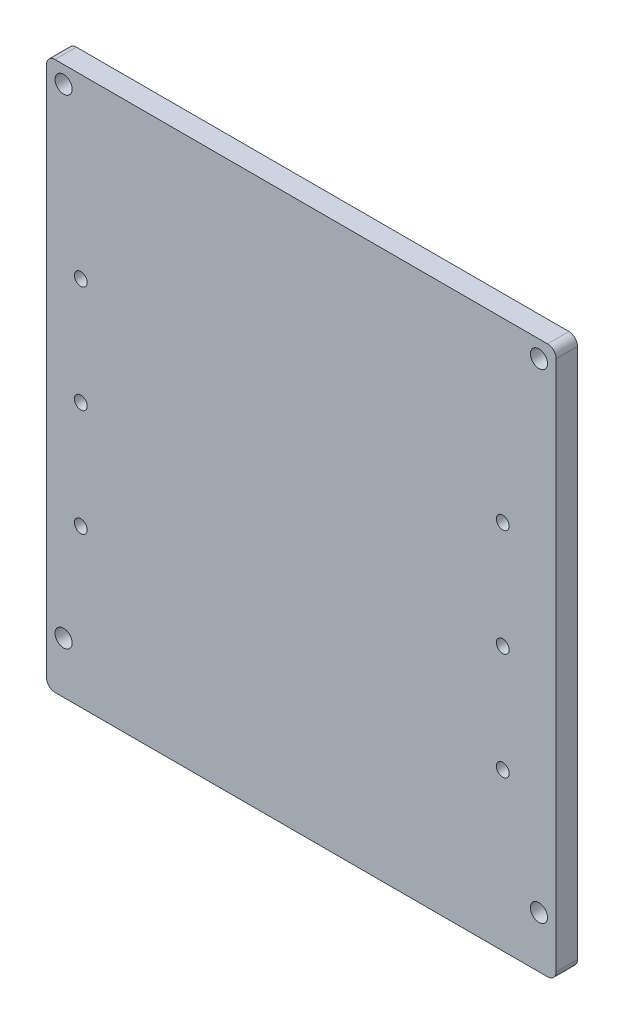
SolidWorks part; units mm, degrees
ref_plane "前视基准面" through (0, 0, 0) normal (0, 0, 1) x (1, 0, 0)
ref_plane "上视基准面" through (0, 0, 0) normal (0, 1, 0) x (1, 0, 0)
ref_plane "右视基准面" through (0, 0, 0) normal (1, 0, 0) x (0, 0, -1)
other "Configuration Table"
sketch "草图1" plane through (0, 0, 0) normal (0, 0, 1) x (1, 0, 0)
  line L8 (62.7093, -58.3451) -> (62.7093, 57.6549)
  line L13 (60.7093, 59.6549) -> (-54.2907, 59.6549)
  line L14 (-56.2907, 57.6549) -> (-56.2907, -58.3451)
  line L15 (-54.2907, -60.3451) -> (60.7093, -60.3451)
  arc A12 (62.7093, 57.6549) -> (60.7093, 59.6549) centre (60.7093, 57.6549) ccw
  arc A13 (-54.2907, 59.6549) -> (-56.2907, 57.6549) centre (-54.2907, 57.6549) ccw
  arc A14 (-56.2907, -58.3451) -> (-54.2907, -60.3451) centre (-54.2907, -58.3451) ccw
  arc A15 (60.7093, -60.3451) -> (62.7093, -58.3451) centre (60.7093, -58.3451) ccw
  circle A16 centre (-52.2907, -56.3451) radius 2
  circle A17 centre (58.7093, -56.3451) radius 2
  circle A18 centre (58.7093, 55.6549) radius 2
  circle A19 centre (-52.2907, 55.6549) radius 2
  point P0 (0, 0)
extrude "凸台-拉伸1" add sketch "草图1" along normal blind 5
sketch "草图5" plane through (0, 0, 3) normal (0, 0, 1) x (1, 0, 0)
  line L36 (-56.2756, 57.6214) -> (-56.2756, -74.02) construction
  line L37 (56.3281, 59.5462) -> (-54.3508, 59.5462) construction
  line L38 (-56.4727, -58.129) -> (58.5273, -58.129) construction
  line L44 (-56.2756, 24.5462) -> (58.253, 24.5462) construction
  line L45 (-56.2756, 57.6214) -> (-56.2756, -74.02) construction
  line L46 (58.253, -74.02) -> (58.253, 57.6214) construction
  line L49 (-31.2756, 59.5462) -> (-31.2756, -58.129) construction
  line L50 (38.253, 59.5462) -> (38.253, -58.129) construction
  line L51 (33.2648, -15.6264) -> (33.2648, 0.4736)
  line L52 (17.1648, -15.6264) -> (33.2648, -15.6264)
  line L53 (17.1648, 0.4736) -> (17.1648, -15.6264)
  line L54 (33.2648, 0.4736) -> (17.1648, 0.4736)
  line L55 (33.2648, 6.3736) -> (33.2648, 22.4736)
  line L56 (17.1648, 6.3736) -> (33.2648, 6.3736)
  line L57 (17.1648, 22.4736) -> (17.1648, 6.3736)
  line L58 (33.2648, 22.4736) -> (17.1648, 22.4736)
  line L59 (11.2648, -15.6264) -> (11.2648, 0.4736)
  line L60 (-4.8352, -15.6264) -> (11.2648, -15.6264)
  line L61 (-4.8352, 0.4736) -> (-4.8352, -15.6264)
  line L62 (11.2648, 0.4736) -> (-4.8352, 0.4736)
  line L63 (-10.7352, 6.3736) -> (-10.7352, 22.4736)
  line L64 (-26.8352, 6.3736) -> (-10.7352, 6.3736)
  line L65 (-26.8352, 22.4736) -> (-26.8352, 6.3736)
  line L66 (-10.7352, 22.4736) -> (-26.8352, 22.4736)
  line L67 (-10.7352, -15.6264) -> (-10.7352, 0.4736)
  line L68 (-26.8352, -15.6264) -> (-10.7352, -15.6264)
  line L69 (-26.8352, 0.4736) -> (-26.8352, -15.6264)
  line L70 (-10.7352, 0.4736) -> (-26.8352, 0.4736)
  line L71 (-10.7352, -37.6264) -> (-10.7352, -21.5264)
  line L72 (-26.8352, -37.6264) -> (-10.7352, -37.6264)
  line L73 (-26.8352, -21.5264) -> (-26.8352, -37.6264)
  line L74 (-10.7352, -21.5264) -> (-26.8352, -21.5264)
  line L75 (11.2648, 6.3736) -> (11.2648, 22.4736)
  line L76 (-4.8352, 6.3736) -> (11.2648, 6.3736)
  line L77 (-4.8352, 22.4736) -> (-4.8352, 6.3736)
  line L78 (11.2648, 22.4736) -> (-4.8352, 22.4736)
  line L79 (11.2648, -37.6264) -> (11.2648, -21.5264)
  line L80 (-4.8352, -37.6264) -> (11.2648, -37.6264)
  line L81 (-4.8352, -21.5264) -> (-4.8352, -37.6264)
  line L82 (11.2648, -21.5264) -> (-4.8352, -21.5264)
  line L83 (33.2648, -37.6264) -> (33.2648, -21.5264)
  line L84 (17.1648, -37.6264) -> (33.2648, -37.6264)
  line L85 (17.1648, -21.5264) -> (17.1648, -37.6264)
  line L86 (33.2648, -21.5264) -> (17.1648, -21.5264)
  line L87 (-56.2756, -40.0764) -> (58.253, -40.0764) construction
  line L88 (33.2648, -58.6264) -> (17.1648, -58.6264)
  line L89 (17.1648, -58.6264) -> (17.1648, -42.5264)
  line L90 (17.1648, -42.5264) -> (33.2648, -42.5264)
  line L91 (33.2648, -42.5264) -> (33.2648, -58.6264)
  line L92 (11.2648, -58.6264) -> (-4.8352, -58.6264)
  line L93 (-4.8352, -58.6264) -> (-4.8352, -42.5264)
  line L94 (-4.8352, -42.5264) -> (11.2648, -42.5264)
  line L95 (11.2648, -42.5264) -> (11.2648, -58.6264)
  line L96 (-10.7352, -58.6264) -> (-26.8352, -58.6264)
  line L97 (-26.8352, -58.6264) -> (-26.8352, -42.5264)
  line L98 (-26.8352, -42.5264) -> (-10.7352, -42.5264)
  line L99 (-10.7352, -42.5264) -> (-10.7352, -58.6264)
  line L100 (58.253, -74.02) -> (58.253, 57.6214) construction
  circle A0 centre (-48.2756, 18.3019) radius 1.5
  circle A1 centre (50.253, 18.3019) radius 1.5
  circle A2 centre (-48.2756, -6.6981) radius 1.5
  circle A3 centre (50.253, -6.6981) radius 1.5
  circle A4 centre (-48.2756, -31.6981) radius 1.5
  circle A5 centre (50.253, -31.6981) radius 1.5
  dimension "D5" = 25
  dimension "D14" = 3
  dimension "D15" = 3
  dimension "D16" = 3
  dimension "D17" = 3
  dimension "D18" = 3
  dimension "D19" = 3
  dimension "D1" = 35
  dimension "D2" = 25
  dimension "D3" = 20
  dimension "D4" = 2.45
  dimension "D6" = 25
  dimension "D7" = 25
  dimension "D8" = 25
  dimension "D9" = 8
  dimension "D10" = 8
  dimension "D11" = 8
  dimension "D12" = 8
  dimension "D13" = 101.6508
extrude "切除-拉伸1" cut sketch "草图5" against normal through all
sketch "草图8" plane through (0, 0, 5) normal (0, 0, 1) x (1, 0, 0)
  line L0 (-26.8352, -42.5264) -> (-26.8352, -58.6264) construction
  line L1 (-56.2907, -58.3451) -> (-26.8352, -58.3451)
  line L2 (-56.2907, -58.3451) -> (-56.2907, -68.3451)
  line L3 (-56.2907, -68.3451) -> (-26.8352, -68.3451)
  line L4 (-26.8352, -58.3451) -> (-26.8352, -60.3451)
  line L5 (-54.2907, -60.3451) -> (60.7093, -60.3451) construction
  line L6 (62.7093, -58.3451) -> (33.2648, -58.3451)
  line L7 (62.7093, -58.3451) -> (62.7093, -68.3451)
  line L8 (62.7093, -68.3451) -> (33.2648, -68.3451)
  line L9 (33.2648, -58.3451) -> (33.2648, -60.3451)
  line L10 (-26.8352, -60.3451) -> (33.2648, -60.3451)
  line L12 (-26.8352, -68.3451) -> (33.2648, -68.3451)
  dimension "D1" = 10
  dimension "D2" = 10
  dimension "D3" = 29.4555
extrude "凸台-拉伸2" add sketch "草图8" against normal blind 5
fillet "圆角1" radius 2 2 edges at (-56.2907, -68.3451, 2.5) (62.7093, -68.3451, 2.5)
sketch "草图9" plane through (0, 0, 0) normal (0, 0, -1) x (-1, 0, 0)
  circle A0 centre (-50.253, -6.6981) radius 1.5 construction
  circle A1 centre (-50.253, -31.6981) radius 1.5 construction
  circle A2 centre (48.2756, -31.6981) radius 1.5 construction
  circle A3 centre (48.2756, -6.6981) radius 1.5 construction
  circle A4 centre (48.2756, 18.3019) radius 1.5 construction
  circle A5 centre (-50.253, 18.3019) radius 1.5 construction
  circle A6 centre (-50.253, -6.6981) radius 1.5
  circle A7 centre (-50.253, -31.6981) radius 1.5
  circle A8 centre (48.2756, -31.6981) radius 1.5
  circle A9 centre (48.2756, -6.6981) radius 1.5
  circle A10 centre (48.2756, 18.3019) radius 1.5
  circle A11 centre (-50.253, 18.3019) radius 1.5
extrude "切除-拉伸2" cut sketch "草图9" against normal blind 10
